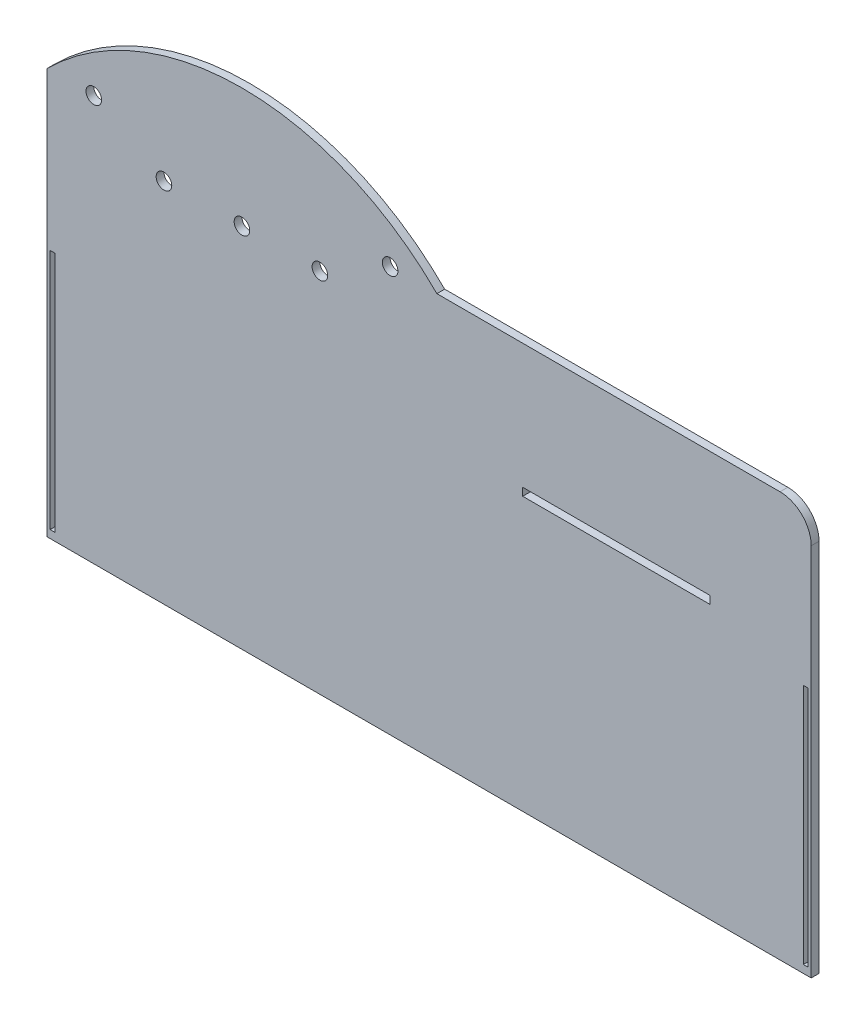
SolidWorks part; units mm, degrees
ref_plane "Alzado" through (0, 0, 0) normal (0, 0, 1) x (1, 0, 0)
ref_plane "Planta" through (0, 0, 0) normal (0, 1, 0) x (1, 0, 0)
ref_plane "Vista lateral" through (0, 0, 0) normal (1, 0, 0) x (0, 0, -1)
sketch "Croquis1" plane through (0, 0, 0) normal (0, 0, 1) x (1, 0, 0)
  line L0 (-311.15, 165.1) -> (6.35, 165.1) construction
  line L1 (6.35, 165.1) -> (311.15, 165.1)
  line L2 (-311.15, 165.1) -> (-311.15, -165.1)
  line L3 (-311.15, -165.1) -> (311.15, -165.1)
  line L4 (311.15, 165.1) -> (311.15, -165.1)
  line L5 (-311.15, 165.1) -> (311.15, -165.1) construction
  line L6 (-311.15, -165.1) -> (311.15, 165.1) construction
  arc A0 (-311.15, 165.1) -> (6.35, 165.1) centre (-152.4, 6.35) cw
  point P0 (0, 0)
  dimension "D4" = 330.2
  dimension "D1" = 622.3
  dimension "D2" = 330.2
  dimension "D3" = 224.5064
  dimension "D5" = 317.5
extrude "Saliente-Extruir1" add sketch "Croquis1" along normal blind 6.35
sketch "Croquis2" plane through (0, 0, 6.35) normal (0, 0, 1) x (1, 0, 0)
  line L0 (311.15, 165.1) -> (6.35, 165.1) construction
  line L1 (76.2, 63.5) -> (228.6, 63.5)
  line L2 (76.2, 63.5) -> (76.2, 57.15)
  line L3 (76.2, 57.15) -> (228.6, 57.15)
  line L4 (228.6, 63.5) -> (228.6, 57.15)
  line L6 (311.15, -165.1) -> (311.15, 165.1) construction
  point P6 (152.4, 63.5)
  dimension "D1" = 152.4
  dimension "D2" = 6.35
  dimension "D3" = 101.6
  dimension "D4" = 158.75
extrude "Cortar-Extruir1" cut sketch "Croquis2" against normal blind 6.35
sketch "Croquis3" plane through (0, 0, 6.35) normal (0, 0, 1) x (1, 0, 0)
  line L0 (-311.15, 165.1) -> (-311.15, -165.1) construction
  line L2 (-152.4, 133.35) -> (-215.9, 133.35) construction
  line L3 (-152.4, 133.35) -> (-88.9, 133.35) construction
  circle A0 centre (-152.4, 133.35) radius 6.35
  circle A1 centre (-215.9, 133.35) radius 6.35
  circle A2 centre (-88.9, 133.35) radius 6.35
  dimension "D3" = 12.7
  dimension "D4" = 12.7
  dimension "D5" = 12.7
  dimension "D1" = 158.75
  dimension "D2" = 31.75
  dimension "D6" = 63.5
  dimension "D7" = 63.5
extrude "Cortar-Extruir2" cut sketch "Croquis3" against normal blind 6.35
sketch "Croquis4" plane through (0, 0, 6.35) normal (0, 0, 1) x (1, 0, 0)
  line L0 (-311.15, 165.1) -> (-273.05, 165.1) construction
  line L1 (6.35, 165.1) -> (-31.75, 165.1) construction
  circle A0 centre (-273.05, 165.1) radius 6.35
  circle A1 centre (-31.75, 165.1) radius 6.35
  dimension "D1" = 12.7
  dimension "D2" = 12.7
  dimension "D3" = 38.1
  dimension "D4" = 38.1
extrude "Cortar-Extruir3" cut sketch "Croquis4" against normal blind 6.35
fillet "Redondeo1" radius 25.4 1 edges at (311.15, 165.1, 3.175)
sketch "Croquis5" plane through (0, 0, 6.35) normal (0, 0, 1) x (1, 0, 0)
  line L1 (-308.61, -158.75) -> (-304.8, -158.75)
  line L2 (-308.61, -158.75) -> (-308.61, 38.1)
  line L3 (-308.61, 38.1) -> (-304.8, 38.1)
  line L4 (-304.8, -158.75) -> (-304.8, 38.1)
  line L6 (-311.15, 58.4945) -> (-308.61, 58.4945) construction
  line L7 (0, 0) -> (0, -66.4786) construction
  line L8 (308.61, -158.75) -> (304.8, -158.75)
  line L9 (308.61, 38.1) -> (304.8, 38.1)
  line L10 (304.8, -158.75) -> (304.8, 38.1)
  line L11 (308.61, -158.75) -> (308.61, 38.1)
  line L12 (-311.15, 165.1) -> (-311.15, -165.1) construction
  line L13 (-311.15, -165.1) -> (311.15, -165.1) construction
  dimension "D1" = 2.54
  dimension "D2" = 3.81
  dimension "D3" = 196.85
  dimension "D4" = 203.2
extrude "Cortar-Extruir4" cut sketch "Croquis5" against normal blind 6.35
